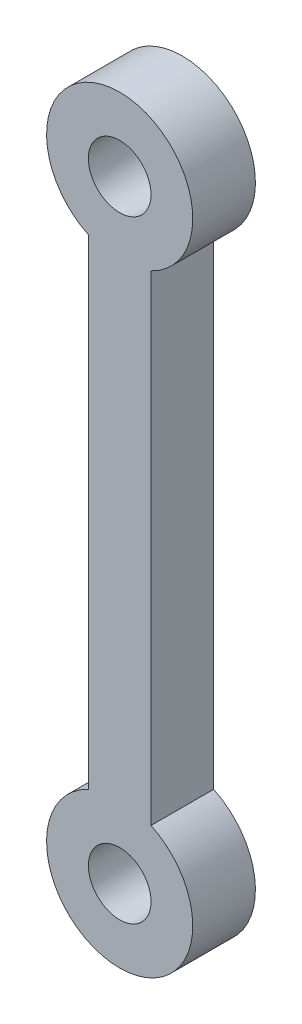
SolidWorks part; units mm, degrees
ref_plane "Piano frontale" through (0, 0, 0) normal (0, 0, 1) x (1, 0, 0)
ref_plane "Piano superiore" through (0, 0, 0) normal (0, 1, 0) x (1, 0, 0)
ref_plane "Piano destro" through (0, 0, 0) normal (1, 0, 0) x (0, 0, -1)
sketch "Schizzo2" plane through (0, 0, 0) normal (0, 0, 1) x (1, 0, 0)
  line L0 (-36.1111, -20.5665) -> (-36.1111, -27.5665)
  line L1 (-34.1111, -27.5665) -> (-34.1111, -50.5665)
  line L2 (-34.1111, -50.5665) -> (-36.1111, -50.5665)
  line L3 (-36.1111, -50.5665) -> (-36.1111, -57.5665)
  line L4 (-36.1111, -57.5665) -> (-29.1111, -57.5665)
  line L5 (-29.1111, -57.5665) -> (-29.1111, -50.5665)
  line L6 (-29.1111, -50.5665) -> (-31.1111, -50.5665)
  line L7 (-31.1111, -50.5665) -> (-31.1111, -27.5665)
  line L8 (-31.1111, -27.5665) -> (-29.1111, -27.5665)
  line L9 (-29.1111, -27.5665) -> (-29.1111, -20.5665)
  line L10 (-29.1111, -20.5665) -> (-36.1111, -20.5665)
  line L11 (-36.1111, -27.5665) -> (-34.1111, -27.5665)
  line L12 (-32.6111, -20.5665) -> (-32.6111, -57.5665) construction
  line L13 (-36.0948, -24.0665) -> (-29.1111, -24.0665) construction
  line L14 (-36.1111, -54.0665) -> (-29.1274, -54.0665) construction
  circle A0 centre (-32.6111, -24.4042) radius 3.5
  circle A1 centre (-32.6111, -53.7288) radius 3.5
  point P22 (0, 0)
  point P23 (-32.6111, -20.5665)
  point P24 (0, 0)
  point P25 (-29.1111, -24.0665)
  point P26 (-36.1111, -54.2165)
  point P27 (-32.6111, -57.5665)
  point P28 (-29.1274, -54.0665)
  point P29 (-31.1111, -27.5665)
  point P30 (-34.1111, -27.5665)
  point P31 (-31.1111, -50.5665)
  point P32 (-29.1274, -54.0665)
  point P33 (-36.1111, -54.0665)
  point P34 (-34.1111, -50.5665)
  point P35 (-31.1111, -50.5665)
  point P37 (-29.1111, -24.0665)
  point P40 (-34.1111, -50.5665)
  dimension "D7" = 7
  dimension "D8" = 7
  dimension "D9" = 3.5
  dimension "D1" = 37
  dimension "D2" = 3
  dimension "D3" = 7
  dimension "D4" = 7
  dimension "D5" = 7
  dimension "D6" = 3.5
extrude "Estrusione-Estrusione2" add sketch "Schizzo2" along normal blind 3 contours A0 L0 | A1 L7 A0 L1 | A1 L3
sketch "Schizzo3" plane through (0, 0, 0) normal (0, 0, 1) x (1, 0, 0)
  line L0 (-32.6111, -20.9042) -> (-32.6111, -57.2288) construction
  line L1 (-36.1111, -24.4042) -> (-29.1111, -24.4042) construction
  line L2 (-36.1111, -53.7288) -> (-29.1111, -53.7288) construction
  arc A0 (-31.1111, -27.5665) -> (-34.1111, -27.5665) centre (-32.6111, -24.4042) ccw construction
  arc A1 (-34.1111, -50.5665) -> (-31.1111, -50.5665) centre (-32.6111, -53.7288) ccw construction
  circle A2 centre (-32.6111, -24.4042) radius 1.5
  circle A3 centre (-32.6111, -53.7288) radius 1.5
  dimension "D1" = 3
  dimension "D2" = 3
extrude "Taglio-Estrusione7" cut sketch "Schizzo3" against normal through all from surface at 3 starting at face at (-32.6111, -39.0665, 3)
